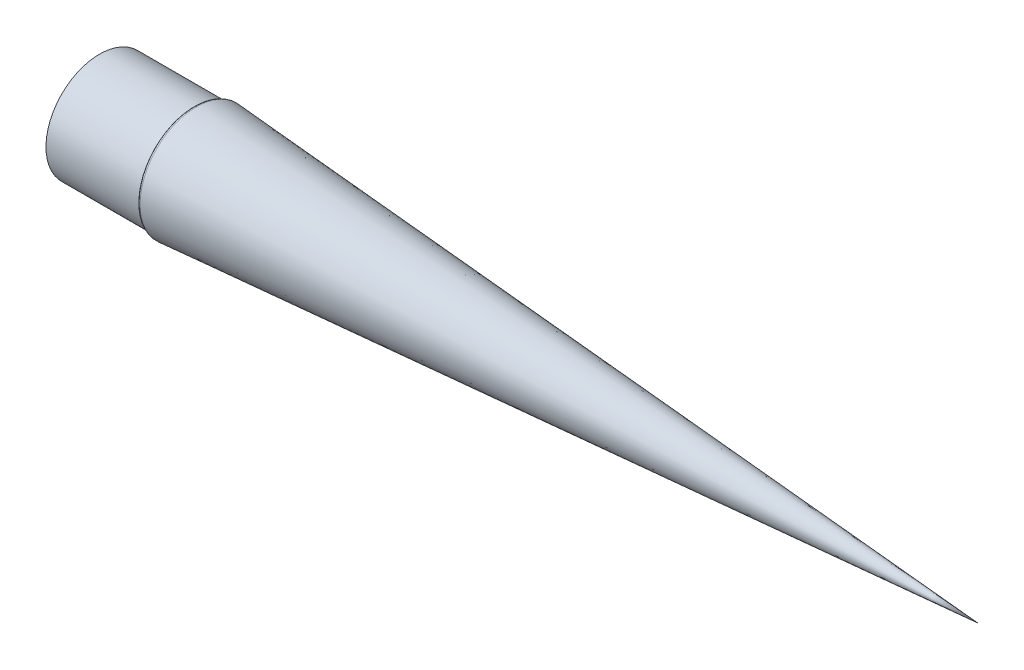
SolidWorks part; units mm, degrees
ref_plane "Front Plane" through (0, 0, 0) normal (0, 0, 1) x (1, 0, 0)
ref_plane "Top Plane" through (0, 0, 0) normal (0, 1, 0) x (1, 0, 0)
ref_plane "Right Plane" through (0, 0, 0) normal (1, 0, 0) x (0, 0, -1)
sketch "Sketch1" plane through (0, 0, 0) normal (0, 0, 1) x (1, 0, 0)
  line L0 (-26.7776, 14.5) -> (-1.3776, 14.5)
  line L2 (-0.5419, 15.265) -> (211.0181, 0)
  line L3 (211.0181, 0) -> (200.4578, 0)
  line L4 (200.4578, 0) -> (-0.5693, 14.505)
  line L6 (-1.3776, 13.74) -> (-26.7776, 13.74)
  line L7 (-26.7776, 13.74) -> (-26.7776, 14.5)
  line L8 (0, 0) -> (344.2537, 0) construction
  arc A0 (-1.3776, 13.74) -> (-0.6186, 14.4614) centre (-1.3776, 14.5) ccw
  arc A1 (-0.6186, 14.4614) -> (-0.5693, 14.505) centre (-0.5726, 14.459) cw
  arc A2 (-1.3776, 14.5) -> (-1.2743, 14.6008) centre (-1.3776, 14.6034) ccw
  arc A3 (-1.2743, 14.6008) -> (-0.5419, 15.265) centre (-0.5911, 14.5833) cw
  point P10 (-1.5816, 14.4079)
  point P11 (-1.8904, 13.7205)
  point P18 (-0.846, 14.0972)
  point P19 (-0.5406, 14.9663)
  point P20 (0, 0)
  point P21 (-1.34, 13.9684)
  point P22 (-1.01, 14.8029)
  point P23 (-4.6144, 14.5)
  point P24 (-2.2578, 13.74)
  point P25 (-2.985, 14.5)
  point P26 (-1.3652, 14.6324)
  point P27 (-1.3282, 13.74)
  point P28 (0, 0)
  point P29 (-0.4445, 14.5)
  point P30 (-1.6535, 14.5)
  point P31 (-1.4393, 14.505)
  point P32 (-0.5911, 14.5)
  point P33 (-1.4393, 13.74)
  point P34 (-1.3776, 13.74)
  dimension "D2" = 0.76
  dimension "D3" = 0.76
  dimension "D4" = 25.4
  dimension "D7" = 13.74
  dimension "D1" = 211.56
  dimension "D5" = 15.265
  dimension "D6" = 14.505
revolve "Revolve1" add sketch "Sketch1" angle 360 about L8
equation "\"D3@Sketch1\"=\"D2@Sketch1\""
